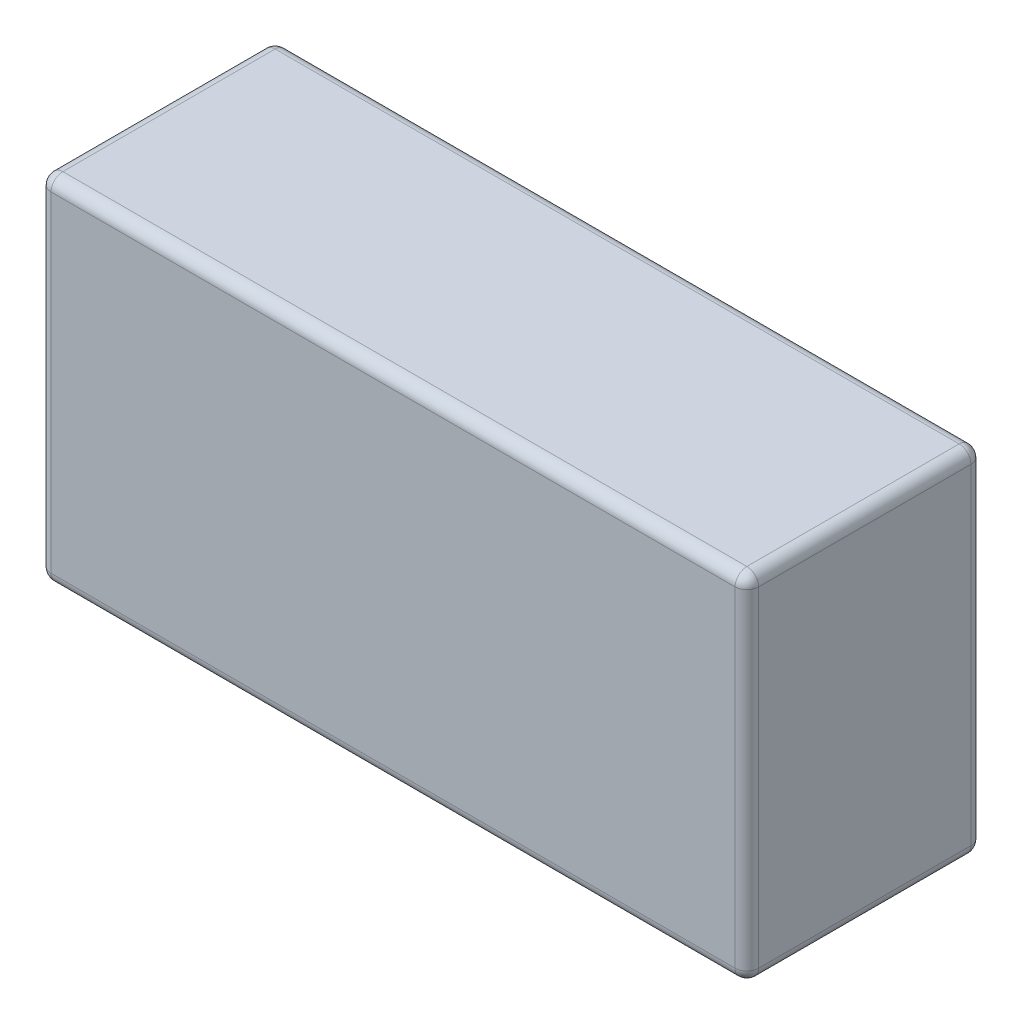
SolidWorks part; units mm, degrees
ref_plane "Alzado" through (0, 0, 0) normal (0, 0, 1) x (1, 0, 0)
ref_plane "Planta" through (0, 0, 0) normal (0, 1, 0) x (1, 0, 0)
ref_plane "Vista lateral" through (0, 0, 0) normal (1, 0, 0) x (0, 0, -1)
sketch "Croquis1" plane through (0, 0, 0) normal (0, 0, 1) x (1, 0, 0)
  line L1 (-30, 15) -> (30, 15)
  line L2 (-30, 15) -> (-30, -15)
  line L3 (-30, -15) -> (30, -15)
  line L4 (30, 15) -> (30, -15)
  line L5 (-30, 15) -> (30, -15) construction
  line L6 (-30, -15) -> (30, 15) construction
  point P0 (0, 0)
  dimension "D1" = 60
  dimension "D2" = 30
extrude "Saliente-Extruir1" add sketch "Croquis1" along normal blind 20
fillet "Redondeo1" radius 1 12 edges at (0, -15, 0) (-30, 0, 0) (-30, -15, 10) (0, -15, 20) (30, 0, 20) (30, 0, 0) (-30, 0, 20) (0, 15, 0) (0, 15, 20) (30, -15, 10) (-30, 15, 10) (30, 15, 10)
